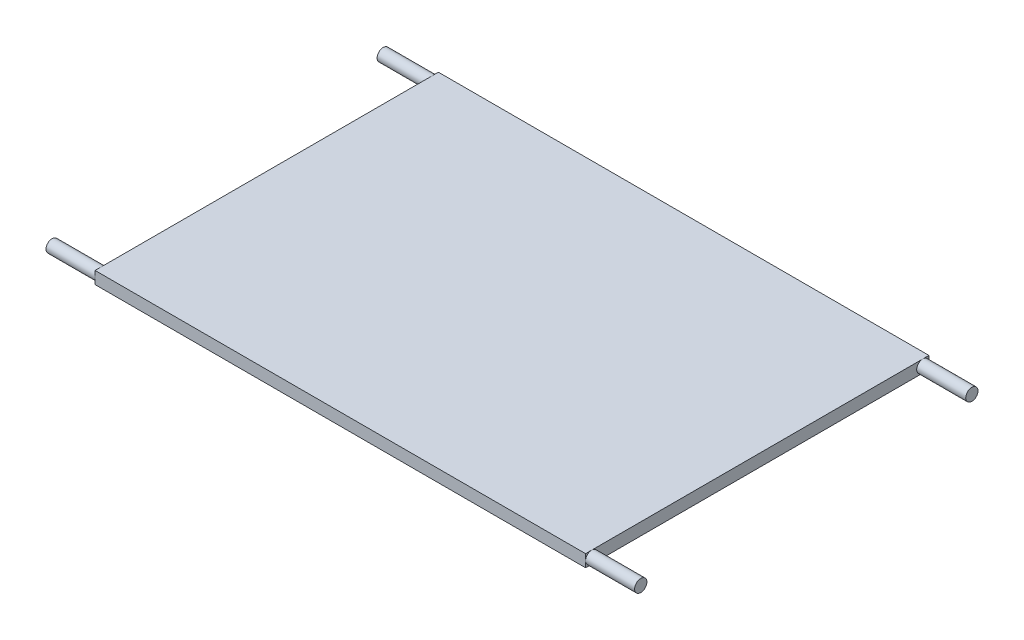
SolidWorks part; units mm, degrees
ref_plane "Plan de face" through (0, 0, 0) normal (0, 0, 1) x (1, 0, 0)
ref_plane "Plan de dessus" through (0, 0, 0) normal (0, 1, 0) x (1, 0, 0)
ref_plane "Plan de droite" through (0, 0, 0) normal (1, 0, 0) x (0, 0, -1)
sketch "Esquisse1" plane through (0, 0, 0) normal (0, 1, 0) x (1, 0, 0)
  line L1 (-100, -70) -> (100, -70)
  line L2 (-100, -70) -> (-100, 70)
  line L3 (-100, 70) -> (100, 70)
  line L4 (100, -70) -> (100, 70)
  line L5 (-100, -70) -> (100, 70) construction
  line L6 (-100, 70) -> (100, -70) construction
  point P0 (0, 0)
  dimension "D1" = 200
  dimension "D2" = 140
extrude "Boss.-Extru.1" add sketch "Esquisse1" along normal blind 5
sketch "Esquisse3" plane through (-100, 0, 0) normal (-1, 0, 0) x (0, 0, 1)
  line L0 (-70, 5) -> (70, 5) construction
  line L2 (70, 5) -> (70, 0) construction
  circle A0 centre (67.5, 2.5) radius 2.5
  dimension "D1" = 5
  dimension "D2" = 2.5
  dimension "D3" = 2.5
extrude "Boss.-Extru.2" add sketch "Esquisse3" along normal blind 20
sketch "Esquisse4" plane through (100, 0, 0) normal (1, 0, 0) x (0, 0, -1)
  line L0 (-70, 5) -> (-70, 0) construction
  line L1 (-70, 0) -> (70, 0) construction
  circle A0 centre (-67.5, 2.5) radius 2.5
  dimension "D1" = 5
  dimension "D2" = 2.5
  dimension "D3" = 2.5
extrude "Boss.-Extru.3" add sketch "Esquisse4" along normal blind 20
sketch "Esquisse6" plane through (-100, 0, 0) normal (-1, 0, 0) x (0, 0, 1)
  circle A0 centre (-67.5, 2.5) radius 2.5
extrude "Boss.-Extru.4" add sketch "Esquisse6" along normal blind 20
sketch "Esquisse8" plane through (100, 0, 0) normal (1, 0, 0) x (0, 0, -1)
  circle A0 centre (67.5, 2.5) radius 2.5
extrude "Boss.-Extru.5" add sketch "Esquisse8" along normal blind 20
